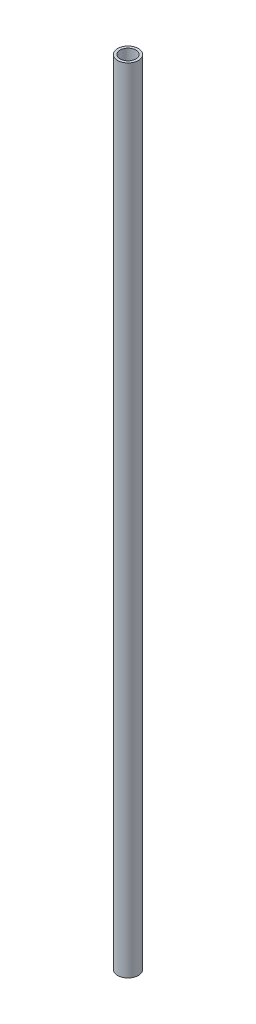
SolidWorks part; units mm, degrees
material "AISI Type 316L stainless steel"
ref_plane "Front Plane" through (0, 0, 0) normal (0, 0, 1) x (1, 0, 0)
ref_plane "Top Plane" through (0, 0, 0) normal (0, 1, 0) x (1, 0, 0)
ref_plane "Right Plane" through (0, 0, 0) normal (1, 0, 0) x (0, 0, -1)
sketch "Sketch1" plane through (0, 0, 0) normal (0, 1, 0) x (1, 0, 0)
  circle A0 centre (0, 0) radius 12.7
  circle A1 centre (0, 0) radius 9.525
  dimension "D1" = 19.05
  dimension "D2" = 25.4
extrude "Boss-Extrude1" add sketch "Sketch1" along normal mid plane 968.375
